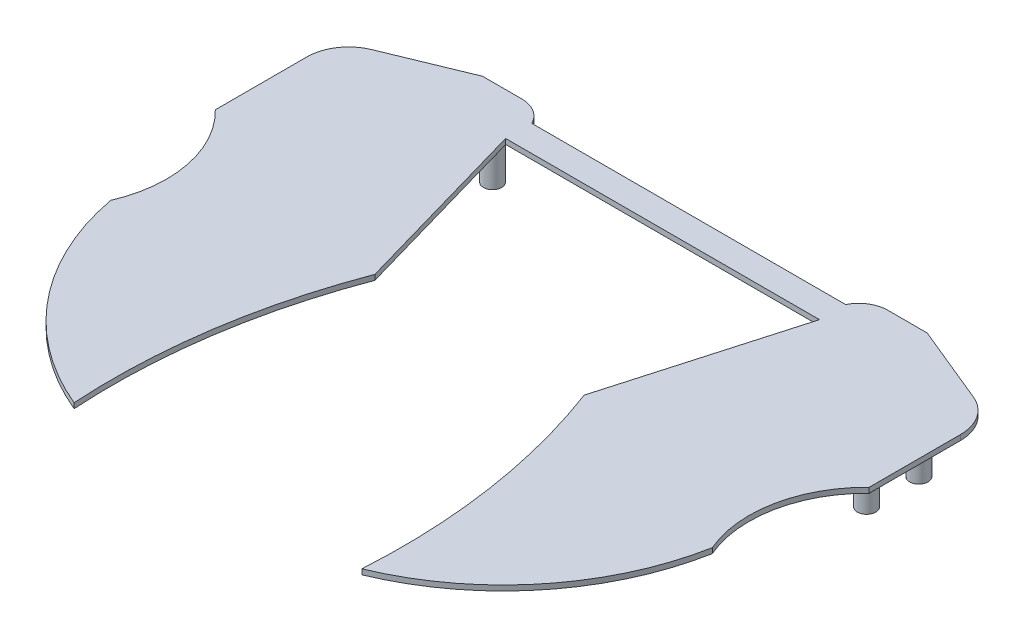
SolidWorks part; units mm, degrees
ref_plane "Front Plane" through (0, 0, 0) normal (0, 0, 1) x (1, 0, 0)
ref_plane "Top Plane" through (0, 0, 0) normal (0, 1, 0) x (1, 0, 0)
ref_plane "Right Plane" through (0, 0, 0) normal (1, 0, 0) x (0, 0, -1)
sketch "Sketch1" plane through (0, 0, 0) normal (0, 1, 0) x (1, 0, 0)
  line L1 (-76.2, -6.35) -> (76.2, -6.35)
  line L2 (-76.2, -6.35) -> (-76.2, 6.35)
  line L3 (-76.2, 6.35) -> (76.2, 6.35)
  line L4 (76.2, -6.35) -> (76.2, 6.35)
  line L5 (-76.2, -6.35) -> (76.2, 6.35) construction
  line L6 (-76.2, 6.35) -> (76.2, -6.35) construction
  point P0 (0, 0)
  dimension "D1" = 152.4
  dimension "D2" = 12.7
extrude "Boss-Extrude1" add sketch "Sketch1" along normal blind 2.54
sketch "Sketch2" plane through (0, 0, 0) normal (0, 1, 0) x (1, 0, 0)
  line L0 (88.9, 14.199) -> (107.95, 14.199)
  line L1 (107.95, 14.199) -> (146.164, -1.5294)
  line L2 (158.75, -20.32) -> (158.75, -64.77)
  line L3 (50.8, -95.25) -> (76.2, -6.35)
  line L4 (76.2, -6.35) -> (76.2, 6.35)
  circle A0 centre (88.9, 0) radius 4.445 construction
  circle A1 centre (138.43, -20.32) radius 4.445 construction
  circle A2 centre (138.43, -45.72) radius 4.445 construction
  arc A3 (76.2, 6.35) -> (88.9, 14.199) centre (88.9, 0) cw
  arc A4 (146.164, -1.5294) -> (158.75, -20.32) centre (138.43, -20.32) cw
  arc A5 (158.75, -64.77) -> (146.05, -128.27) centre (198.5783, -105.7557) ccw
  arc A6 (146.05, -128.27) -> (69.85, -222.25) centre (21.2127, -104.9324) cw
  arc A7 (69.85, -222.25) -> (50.8, -95.25) centre (-234.3383, -202.9495) ccw
  dimension "D4" = 8.89
  dimension "D12" = 304.8
  dimension "D16" = 127
  dimension "D17" = 57.15
  dimension "D1" = 49.53
  dimension "D2" = 20.32
  dimension "D3" = 25.4
  dimension "D5" = 88.9
  dimension "D6" = 19.05
  dimension "D7" = 20.32
  dimension "D8" = 88.9
  dimension "D9" = 25.4
  dimension "D10" = 127
  dimension "D11" = 19.05
  dimension "D13" = 12.7
  dimension "D14" = 63.5
  dimension "D15" = 44.45
extrude "Boss-Extrude2" add sketch "Sketch2" along normal blind 2.54
mirror "Mirror1" about plane through (0, 0, 0) normal (1, 0, 0) of "Boss-Extrude2"
sketch "Sketch3" plane through (0, 0, 0) normal (0, -1, 0) x (1, 0, 0)
  line L0 (0, 0) -> (0, 181.4475) construction
  circle A0 centre (88.9, 0) radius 4.445
  circle A1 centre (138.43, 20.32) radius 4.445
  circle A2 centre (138.43, 45.72) radius 4.445
  circle A3 centre (138.43, 45.72) radius 4.445 construction
  circle A4 centre (138.43, 20.32) radius 4.445 construction
  circle A5 centre (88.9, 0) radius 4.445 construction
  circle A6 centre (-138.43, 45.72) radius 4.445
  circle A7 centre (-138.43, 20.32) radius 4.445
  circle A8 centre (-88.9, 0) radius 4.445
extrude "Boss-Extrude3" add sketch "Sketch3" along normal blind 25.4
